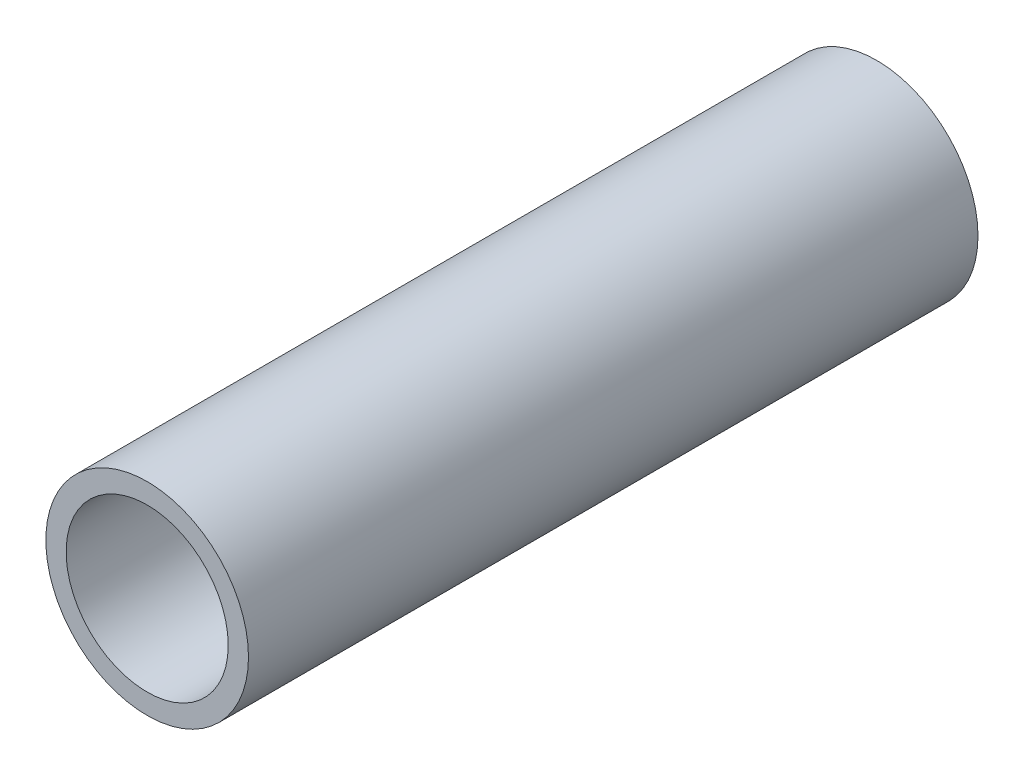
SolidWorks part; units mm, degrees
ref_plane "Front Plane" through (0, 0, 0) normal (0, 0, 1) x (1, 0, 0)
ref_plane "Top Plane" through (0, 0, 0) normal (0, 1, 0) x (1, 0, 0)
ref_plane "Right Plane" through (0, 0, 0) normal (1, 0, 0) x (0, 0, -1)
sketch "Sketch1" plane through (0, 0, 0) normal (0, 0, 1) x (1, 0, 0)
  circle A0 centre (0, 0) radius 1
  circle A1 centre (0, 0) radius 1.25
  dimension "D1" = 2
  dimension "D2" = 2.5
extrude "Tube DIP Body" add sketch "Sketch1" along normal blind 9
